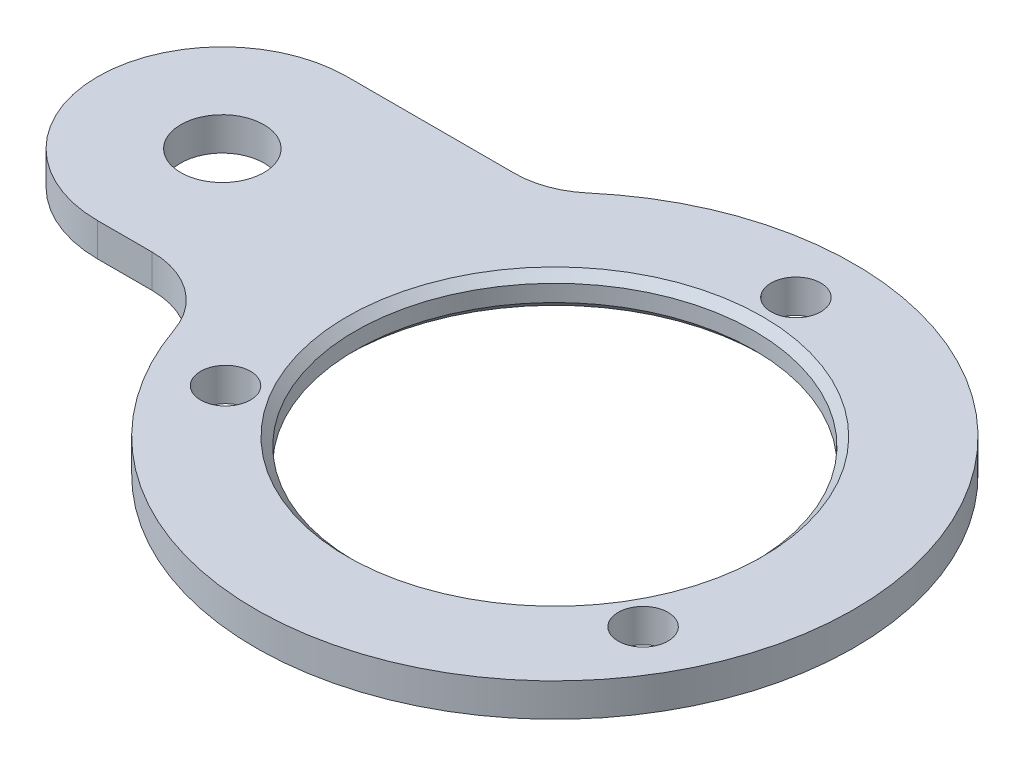
SolidWorks part; units mm, degrees
ref_plane "Face" through (0, 0, 0) normal (0, 0, 1) x (1, 0, 0)
ref_plane "Dessus" through (0, 0, 0) normal (0, 1, 0) x (1, 0, 0)
ref_plane "Droite" through (0, 0, 0) normal (1, 0, 0) x (0, 0, -1)
sketch "Esquisse1" plane through (0, 0, 0) normal (0, 1, 0) x (1, 0, 0)
  line L0 (0, 0) -> (0, 5) construction
  line L1 (0, 0) -> (18, 0) construction
  line L2 (0, 0) -> (0, 18) construction
  line L5 (-25, -2.5) -> (-21.7428, -2.5)
  line L6 (-25, 12.5) -> (-14.9248, 12.5)
  arc A0 (-17.0161, -5.8696) -> (-11.6803, 13.6957) centre (0, 0) ccw
  arc A1 (-11.6803, 13.6957) -> (-14.9248, 12.5) centre (-14.9248, 17.5) cw
  circle A2 centre (0, 0) radius 12
  arc A3 (-25, -2.5) -> (-25, 12.5) centre (-25, 5) cw
  circle A4 centre (-12.5574, -7.25) radius 1.5
  circle A5 centre (12.5574, -7.25) radius 1.5
  circle A6 centre (0, 14.5) radius 1.5
  circle A7 centre (-25, 5) radius 2.5
  arc A8 (-17.0161, -5.8696) -> (-21.7428, -2.5) centre (-21.7428, -7.5) ccw
  dimension "D1" = 5
  dimension "D2" = 5
extrude "Extrusion1" add sketch "Esquisse1" along normal blind 2
chamfer "Chanfrein1" distance 0.5 angle 45 2 edges at (0, 2, 12) (0, 0, 12)
